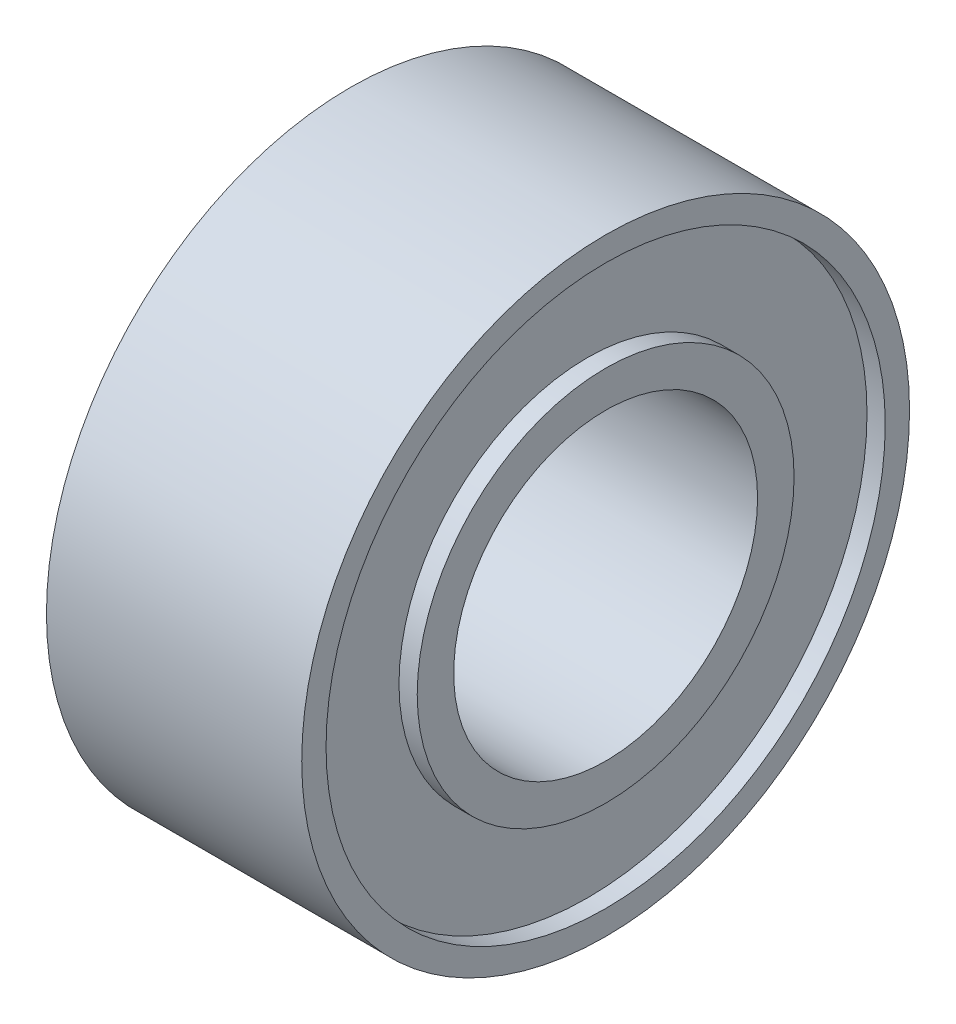
SolidWorks part; units mm, degrees
material "Plain Carbon Steel"
ref_plane "Front Plane" through (0, 0, 0) normal (0, 0, 1) x (1, 0, 0)
ref_plane "Top Plane" through (0, 0, 0) normal (0, 1, 0) x (1, 0, 0)
ref_plane "Right Plane" through (0, 0, 0) normal (1, 0, 0) x (0, 0, -1)
sketch "Sketch1" plane through (0, 0, 0) normal (0, 0, 1) x (1, 0, 0)
  line L0 (2.1, 2.5) -> (-2.1, 2.5)
  line L1 (-2.1, 2.5) -> (-2.1, 3.1)
  line L2 (-2.1, 3.1) -> (-1.8, 3.1)
  line L3 (-1.8, 3.1) -> (-1.8, 4.6)
  line L4 (-1.8, 4.6) -> (-2.1, 4.6)
  line L5 (-2.1, 4.6) -> (-2.1, 5)
  line L6 (-2.1, 5) -> (2.1, 5)
  line L7 (0, 5) -> (0, 2.5) construction
  line L8 (2.1, 4.6) -> (2.1, 5)
  line L9 (1.8, 4.6) -> (2.1, 4.6)
  line L10 (1.8, 3.1) -> (1.8, 4.6)
  line L11 (2.1, 3.1) -> (1.8, 3.1)
  line L12 (2.1, 2.5) -> (2.1, 3.1)
  line L13 (0, 0) -> (-4.3663, 0) construction
  dimension "D1" = 5
  dimension "D2" = 10
  dimension "D3" = 4.2
  dimension "D4" = 6.2
  dimension "D5" = 1.5
  dimension "D6" = 0.3
revolve "Revolve1" add sketch "Sketch1" angle 360 about L13
